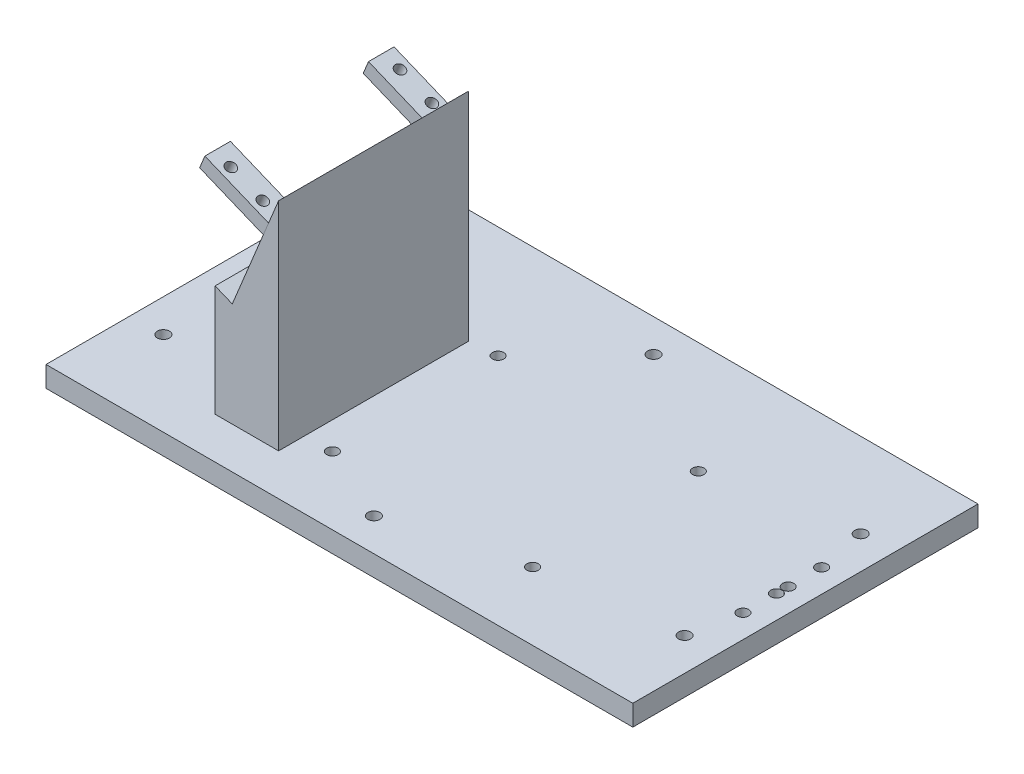
SolidWorks part; units mm, degrees
ref_plane "Front Plane" through (0, 0, 0) normal (0, 0, 1) x (1, 0, 0)
ref_plane "Top Plane" through (0, 0, 0) normal (0, 1, 0) x (1, 0, 0)
ref_plane "Right Plane" through (0, 0, 0) normal (1, 0, 0) x (0, 0, -1)
sketch "Sketch1" plane through (0, 0, 0) normal (0, 1, 0) x (1, 0, 0)
  line L1 (-85, -50) -> (85, -50)
  line L2 (-85, -50) -> (-85, 50)
  line L3 (-85, 50) -> (85, 50)
  line L4 (85, -50) -> (85, 50)
  line L5 (-85, -50) -> (85, 50) construction
  line L6 (-85, 50) -> (85, -50) construction
  point P0 (0, 0)
  dimension "D1" = 170
  dimension "D2" = 100
extrude "Boss-Extrude1" add sketch "Sketch1" along normal blind 6
sketch "Sketch2" plane through (0, 0, 0) normal (0, 0, 1) x (1, 0, 0)
  line L0 (-29.6173, 68.7579) -> (-29.6173, 6)
  line L1 (-27.8088, 73.1501) -> (-31.4259, 64.3657) construction
  line L2 (85, 6) -> (-85, 6) construction
  line L3 (-29.6173, 6) -> (-48.0103, 6)
  line L4 (-48.0103, 6) -> (-48.0103, 38.2101)
  line L5 (-43.0388, 36.163) -> (-61.5323, 43.778) construction
  line L6 (-48.0103, 38.2101) -> (-43.0388, 36.163)
  line L7 (-43.0388, 36.163) -> (-29.6173, 68.7579)
extrude "Boss-Extrude2" add sketch "Sketch2" against normal blind 17 and the other way blind 38
sketch "Sketch3" plane through (-49.5314, 20.3953, 0) normal (-0.9247, 0.3807, 0) x (0, 0, 1)
  line L0 (30.51, 44.5521) -> (30.51, 17.0521) construction
  line L1 (37.91, 44.5521) -> (30.51, 44.5521)
  line L2 (37.91, 44.5521) -> (37.91, 40.5521)
  line L3 (37.91, 40.5521) -> (30.51, 40.5521)
  line L4 (30.51, 44.5521) -> (30.51, 40.5521)
  line L5 (-9.49, 44.5521) -> (-9.49, 17.0521) construction
  line L6 (-16.89, 44.5521) -> (-9.49, 44.5521)
  line L7 (-16.89, 44.5521) -> (-16.89, 40.5521)
  line L8 (-16.89, 40.5521) -> (-9.49, 40.5521)
  line L9 (-9.49, 44.5521) -> (-9.49, 40.5521)
  dimension "D1" = 4
extrude "Boss-Extrude3" add sketch "Sketch3" along normal up to surface (20 mm away)
sketch "Sketch5" plane through (15.4402, 37.4977, 0) normal (-0.3807, -0.9247, 0) x (0.9247, -0.3807, 0)
  circle A0 centre (-68.5661, -13.99) radius 1.45 construction
  circle A1 centre (-68.5661, -13.99) radius 1.45
  circle A2 centre (-68.5661, 35.01) radius 1.45 construction
  circle A3 centre (-58.5661, 35.01) radius 1.45 construction
  circle A4 centre (-58.5661, -13.99) radius 1.45 construction
  circle A5 centre (-68.5661, 35.01) radius 1.45
  circle A6 centre (-58.5661, 35.01) radius 1.45
  circle A7 centre (-58.5661, -13.99) radius 1.45
extrude "Cut-Extrude1" cut sketch "Sketch5" against normal blind 10
extrude "Cut-Extrude2" cut sketch "Sketch6" against normal blind 20
sketch "Sketch6" plane through (145.9671, 0, -60.7675) normal (0, -1, 0) x (0, 0, 1)
  line L0 (35.2675, 221.4671) -> (86.2675, 221.4671) construction
  line L1 (86.2675, 221.4671) -> (86.2675, 70.4671) construction
  line L2 (86.2675, 70.4671) -> (35.2675, 70.4671) construction
  line L3 (35.2675, 70.4671) -> (35.2675, 221.4671) construction
  circle A0 centre (35.2675, 221.4671) radius 1.75
  circle A1 centre (86.2675, 221.4671) radius 1.75
  circle A2 centre (101.2675, 145.4671) radius 1.75
  circle A3 centre (20.2675, 145.4671) radius 1.75
  circle A4 centre (35.2675, 70.4671) radius 1.75
  circle A5 centre (86.2675, 70.4671) radius 1.75
sketch "Sketch7" plane through (0, 6, 0) normal (0, 1, 0) x (1, 0, 0)
  circle A0 centre (36.2981, -30.336) radius 1.65 construction
  circle A1 centre (36.2981, 17.664) radius 1.65 construction
  circle A2 centre (-21.7019, 17.664) radius 1.65 construction
  circle A3 centre (-21.7019, -30.336) radius 1.65 construction
  circle A4 centre (36.2981, -30.336) radius 1.65
  circle A5 centre (36.2981, 17.664) radius 1.65
  circle A6 centre (-21.7019, 17.664) radius 1.65
  circle A7 centre (-21.7019, -30.336) radius 1.65
extrude "Cut-Extrude3" cut sketch "Sketch7" against normal blind 10
sketch "Sketch9" plane through (0, 6, 0) normal (0, 1, 0) x (1, 0, 0)
  circle A0 centre (78.25, -11.34) radius 1.65
  circle A1 centre (78.25, 1.76) radius 1.65
  circle A2 centre (78.25, 11.44) radius 1.65
  circle A3 centre (78.25, -1.66) radius 1.65
extrude "Cut-Extrude6" cut sketch "Sketch9" against normal blind 6
